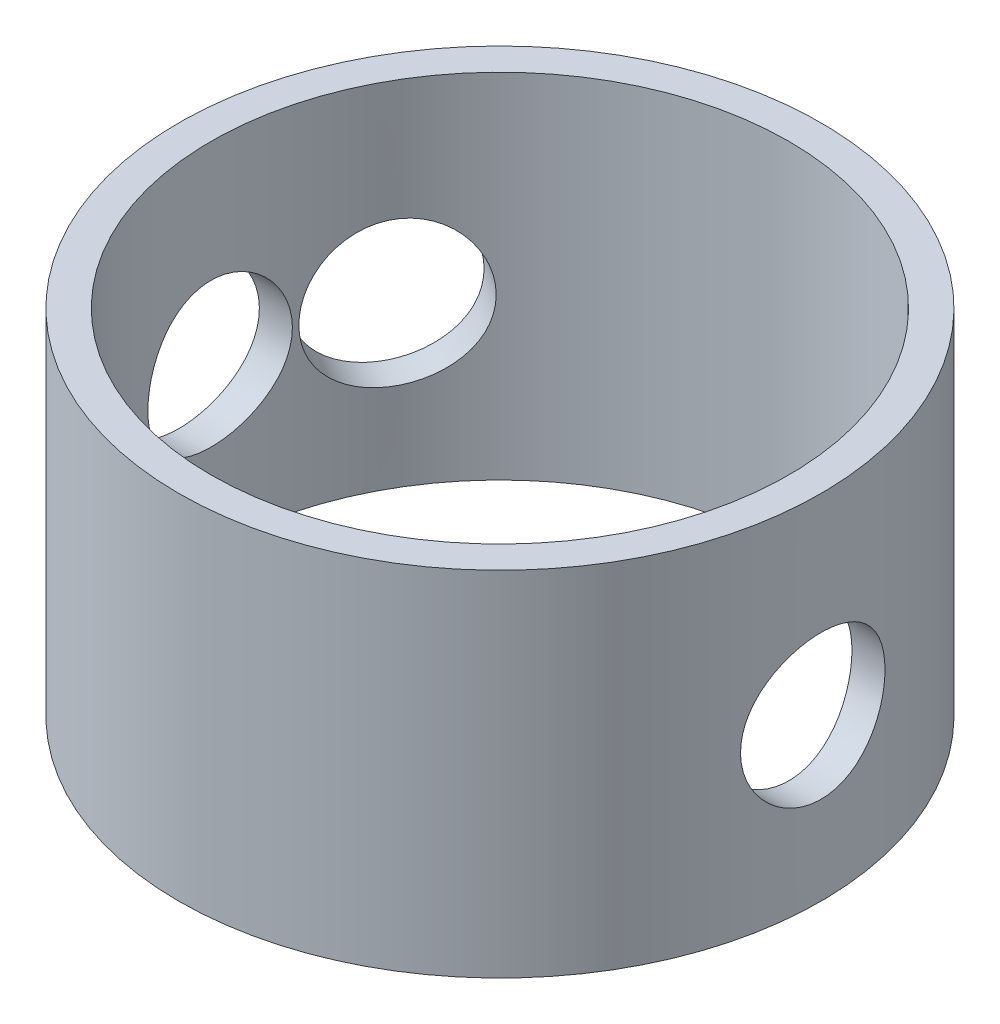
SolidWorks part; units mm, degrees
material "PTFE (geral)"
ref_plane "Plano frontal" through (0, 0, 0) normal (0, 0, 1) x (1, 0, 0)
ref_plane "Plano superior" through (0, 0, 0) normal (0, 1, 0) x (1, 0, 0)
ref_plane "Plano direito" through (0, 0, 0) normal (1, 0, 0) x (0, 0, -1)
sketch "Esboço1" plane through (0, 0, 0) normal (0, 1, 0) x (1, 0, 0)
  line L0 (-22.3434, 0) -> (22.3434, 0) construction
  line L1 (0, 0) -> (-8.6603, 5) construction
  circle A0 centre (0, 0) radius 9
  circle A1 centre (0, 0) radius 10
  point P7 (0, 0)
  dimension "D1" = 18
  dimension "D2" = 20
  dimension "D3" = 30
extrude "Ressalto-extrusão1" add sketch "Esboço1" along normal blind 6 and the other way blind 5
ref_plane "Plano1" through (-8.6603, 0, -5) normal (-0.866, 0, -0.5) x (-0.5, 0, 0.866)
sketch "Esboço2" plane through (-8.6603, 0, -5) normal (-0.866, 0, -0.5) x (-0.5, 0, 0.866)
  circle A0 centre (0, 0) radius 2.25
  dimension "D1" = 4.5
extrude "Corte-extrusão1" cut sketch "Esboço2" against normal up to next
sketch "Esboço3" plane through (0, 0, 0) normal (1, 0, 0) x (0, 0, -1)
  circle A0 centre (0, 0) radius 2.25
  dimension "D1" = 4.5
extrude "Corte-extrusão2" cut sketch "Esboço3" against normal through all both and the other way through all contours A0
